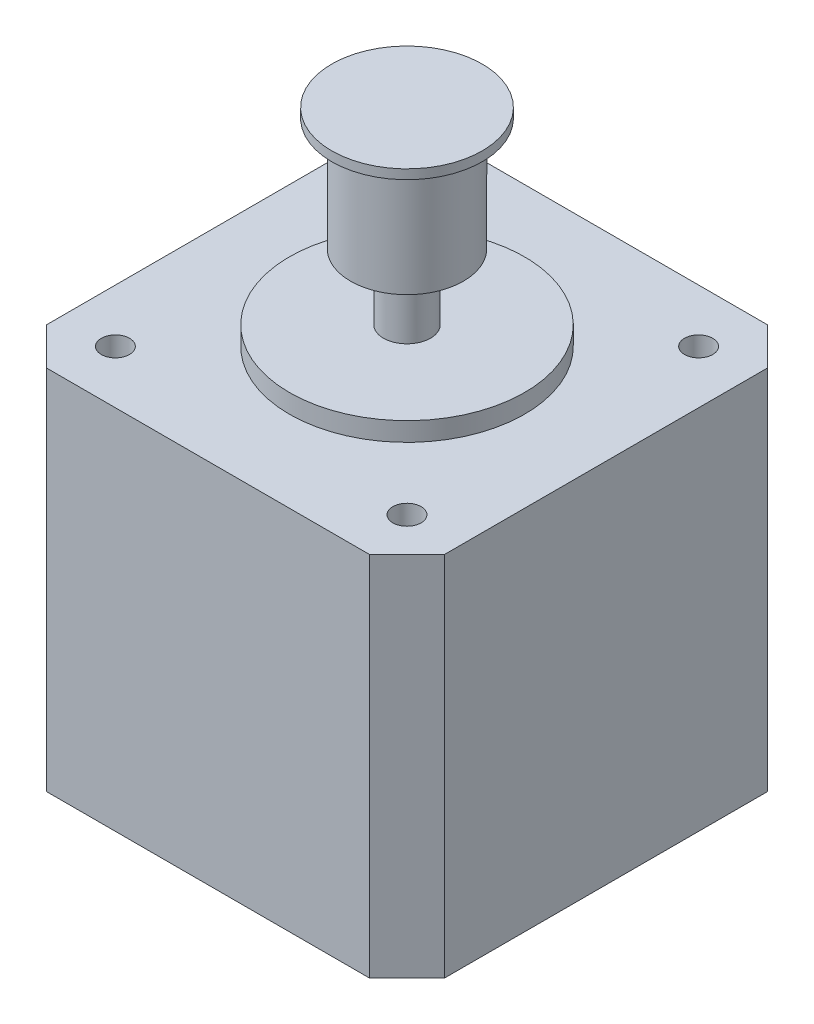
SolidWorks part; units mm, degrees
ref_plane "Alzado" through (0, 0, 0) normal (0, 0, 1) x (1, 0, 0)
ref_plane "Planta" through (0, 0, 0) normal (0, 1, 0) x (1, 0, 0)
ref_plane "Vista lateral" through (0, 0, 0) normal (1, 0, 0) x (0, 0, -1)
sketch "Croquis1" plane through (0, 0, 0) normal (0, 1, 0) x (1, 0, 0)
  line L0 (0, 0) -> (0, 29.15) construction
  line L11 (-15.5, -15.5) -> (15.5, 15.5) construction
  line L12 (-15.5, 15.5) -> (15.5, -15.5) construction
  line L13 (0, 0) -> (29.15, 0) construction
  line L34 (-21.15, 21.15) -> (21.15, 21.15)
  line L35 (-21.15, 21.15) -> (-21.15, -21.15)
  line L36 (-21.15, -21.15) -> (21.15, -21.15)
  line L37 (21.15, 21.15) -> (21.15, -21.15)
  line L38 (-21.15, 21.15) -> (21.15, -21.15) construction
  line L39 (-21.15, -21.15) -> (21.15, 21.15) construction
  circle A0 centre (15.5, 15.5) radius 1.5
  circle A1 centre (15.5, -15.5) radius 1.5
  circle A2 centre (-15.5, -15.5) radius 1.5
  circle A3 centre (-15.5, 15.5) radius 1.5
  point P0 (0, 0)
  point P6 (0, 0)
  point P43 (0, 0)
  dimension "D5" = 3
  dimension "D1" = 42.3
  dimension "D2" = 42.3
  dimension "D3" = 31
  dimension "D4" = 31
  dimension "D6" = 8
  dimension "D7" = 8
  dimension "D8" = 21.9203
  dimension "D9" = 31
extrude "Saliente-Extruir1" add sketch "Croquis1" along normal mid plane 39
sketch "Croquis2" plane through (0, 19.5, 0) normal (0, 1, 0) x (1, 0, 0)
  circle A0 centre (0, 0) radius 12.5
  dimension "D1" = 25
extrude "Saliente-Extruir2" add sketch "Croquis2" along normal blind 2
sketch "Croquis3" plane through (0, 21.5, 0) normal (0, 1, 0) x (1, 0, 0)
  circle A0 centre (0, 0) radius 2.5
  dimension "D1" = 5
extrude "Saliente-Extruir3" add sketch "Croquis3" along normal blind 20
sketch "Croquis4" plane through (0, 41.5, 0) normal (0, 1, 0) x (1, 0, 0)
  circle A0 centre (0, 0) radius 8
  dimension "D1" = 16
extrude "Saliente-Extruir4" add sketch "Croquis4" against normal blind 1 contours A0
sketch "Croquis5" plane through (0, 40.5, 0) normal (0, -1, 0) x (1, 0, 0)
  circle A0 centre (0, 0) radius 6
  dimension "D1" = 12
extrude "Saliente-Extruir5" add sketch "Croquis5" along normal blind 12
chamfer "Chaflán1" distance 4 angle 45 4 edges at (-21.15, 0, 21.15) (21.15, 0, 21.15) (-21.15, 0, -21.15) (21.15, 0, -21.15)
